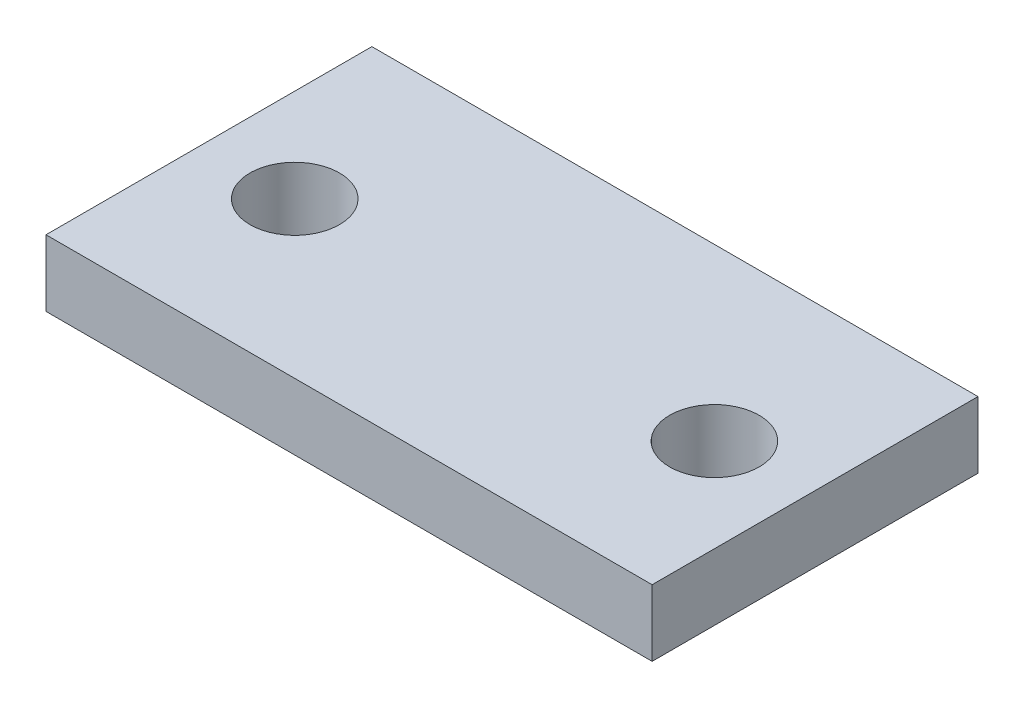
SolidWorks part; units mm, degrees
ref_plane "Front Plane" through (0, 0, 0) normal (0, 0, 1) x (1, 0, 0)
ref_plane "Top Plane" through (0, 0, 0) normal (0, 1, 0) x (1, 0, 0)
ref_plane "Right Plane" through (0, 0, 0) normal (1, 0, 0) x (0, 0, -1)
sketch "Sketch1" plane through (0, 0, 0) normal (0, 1, 0) x (1, 0, 0)
  line L1 (-109.9134, 56.0607) -> (-18.646, 56.0607)
  line L2 (-109.9134, 56.0607) -> (-109.9134, 6.9923)
  line L3 (-109.9134, 6.9923) -> (-18.646, 6.9923)
  line L4 (-18.646, 56.0607) -> (-18.646, 6.9923)
  line L5 (-109.9134, 56.0607) -> (-18.646, 6.9923) construction
  line L6 (-109.9134, 6.9923) -> (-18.646, 56.0607) construction
  point P0 (-64.2797, 31.5265)
extrude "Boss-Extrude1" add sketch "Sketch1" along normal blind 10
sketch "Sketch2" plane through (0, 10, 0) normal (0, 1, 0) x (1, 0, 0)
  circle A0 centre (-95.8753, 30.4085) radius 6.7424
extrude "Cut-Extrude2" cut sketch "Sketch2" against normal blind 10
ref_plane "Plane1" through (-64.2797, 0, 0) normal (-1, 0, 0) x (0, 0, 1)
mirror "Mirror1" about plane through (-64.2797, 0, 0) normal (-1, 0, 0) of "Cut-Extrude2"
